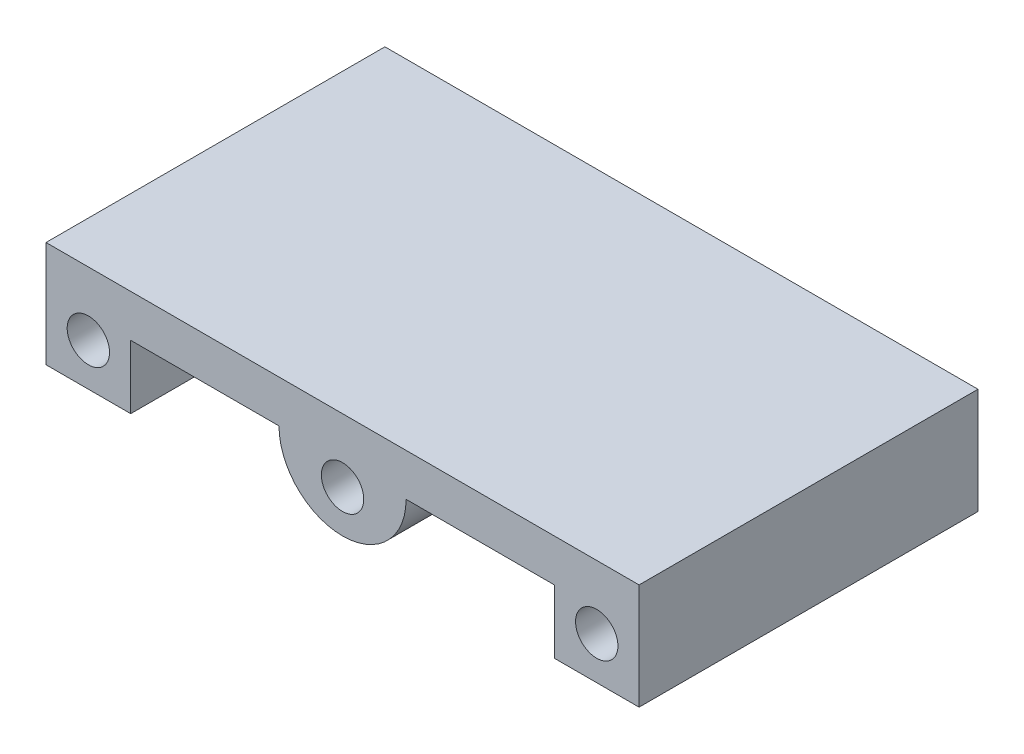
SolidWorks part; units mm, degrees
material "6061-T6 (SS)"
ref_plane "Front Plane" through (0, 0, 0) normal (0, 0, 1) x (1, 0, 0)
ref_plane "Top Plane" through (0, 0, 0) normal (0, 1, 0) x (1, 0, 0)
ref_plane "Right Plane" through (0, 0, 0) normal (1, 0, 0) x (0, 0, -1)
sketch "Sketch1" plane through (0, 0, 0) normal (0, 1, 0) x (1, 0, 0)
  line L1 (-88.9, -50.8) -> (88.9, -50.8)
  line L2 (-88.9, -50.8) -> (-88.9, 50.8)
  line L3 (-88.9, 50.8) -> (88.9, 50.8)
  line L4 (88.9, -50.8) -> (88.9, 50.8)
  line L5 (-88.9, -50.8) -> (88.9, 50.8) construction
  line L6 (-88.9, 50.8) -> (88.9, -50.8) construction
  point P0 (0, 0)
  dimension "D1" = 101.6
  dimension "D2" = 177.8
extrude "Boss-Extrude1" add sketch "Sketch1" along normal blind 12.7
sketch "Sketch2" plane through (0, 0, 50.8) normal (0, 0, 1) x (1, 0, 0)
  line L1 (-88.9, 0) -> (88.9, 0) construction
  line L2 (-19.05, 0) -> (19.05, 0)
  arc A0 (-19.05, 0) -> (19.05, 0) centre (0, 0) ccw
  dimension "D1" = 38.1
extrude "Boss-Extrude2" add sketch "Sketch2" against normal up to surface (101.6 mm away) up to face at (0, 6.35, -50.8)
sketch "Sketch3" plane through (0, 0, 50.8) normal (0, 0, 1) x (1, 0, 0)
  line L0 (0, 0) -> (0, -6.35) construction
  circle A1 centre (0, -6.35) radius 6.35
  point P4 (0, -3.175)
  dimension "D2" = 12.7
  dimension "D1" = 6.35
extrude "Cut-Extrude1" cut sketch "Sketch3" against normal up to surface (101.6 mm away) up to face at (0, 1.0583, -50.8)
sketch "Sketch4" plane through (0, 0, 50.8) normal (0, 0, 1) x (1, 0, 0)
  line L0 (-88.9, 0) -> (-19.05, 0) construction
  line L3 (-88.9, 0) -> (-88.9, -19.05)
  line L4 (-88.9, -19.05) -> (-63.5, -19.05)
  line L5 (-63.5, -19.05) -> (-63.5, 0)
  line L6 (-63.5, 0) -> (-88.9, 0)
  point P0 (-76.2, 0)
  point P4 (0, 0)
  dimension "D3" = 19.05
  dimension "D2" = 76.2
  dimension "D4" = 25.4
extrude "Boss-Extrude3" add sketch "Sketch4" against normal up to surface (101.6 mm away) up to face at (6.35, -6.35, -50.8)
mirror "Mirror1" about plane through (0, 0, 0) normal (1, 0, 0) of "Boss-Extrude3"
sketch "Sketch5" plane through (0, 0, 50.8) normal (0, 0, 1) x (1, 0, 0)
  circle A0 centre (-76.2, -6.35) radius 6.35
  circle A1 centre (76.2, -6.35) radius 6.35
  point P0 (-76.2, -6.35)
  point P1 (76.2, -6.35)
  dimension "D1" = 76.2
  dimension "D2" = 76.2
  dimension "D3" = 6.35
extrude "Cut-Extrude2" cut sketch "Sketch5" against normal up to surface (101.6 mm away) up to face at (6.35, -6.35, -50.8)
